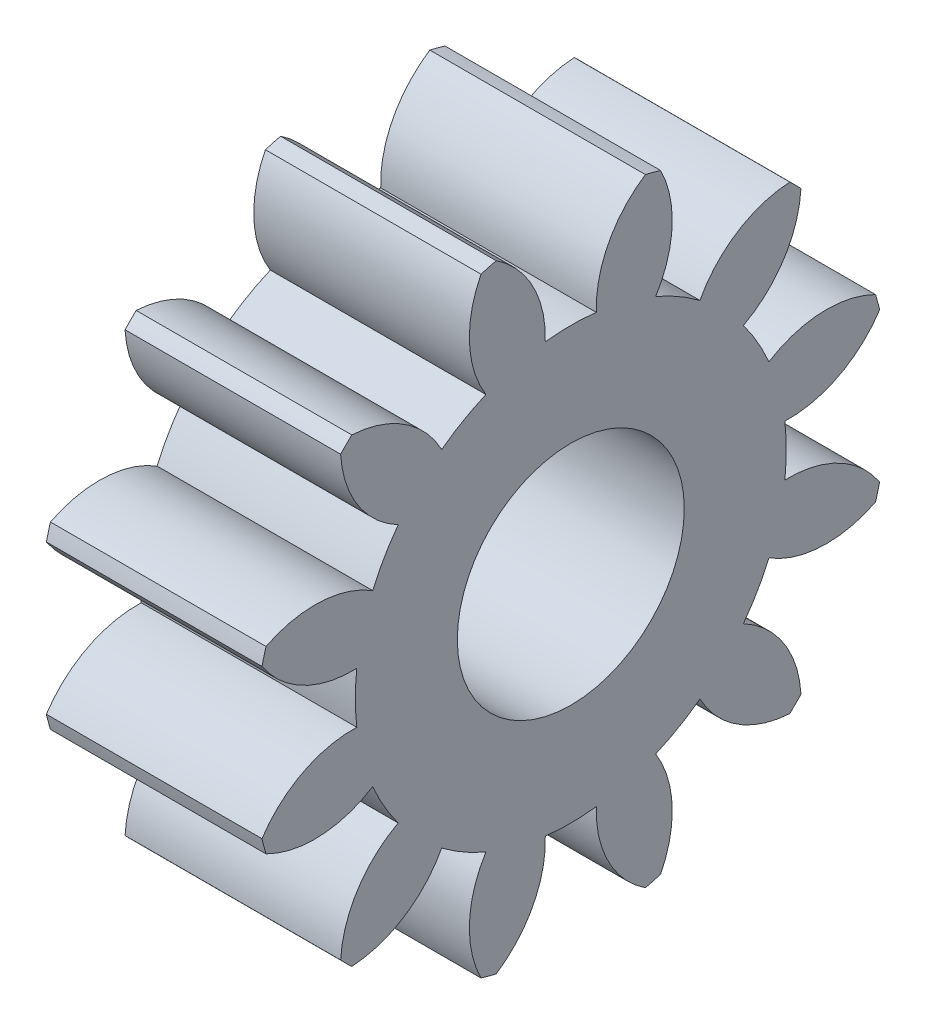
SolidWorks part; units mm, degrees
ref_plane "Plane1" through (0, 0, 0) normal (0, 0, 1) x (1, 0, 0)
ref_plane "Plane2" through (0, 0, 0) normal (0, 1, 0) x (1, 0, 0)
ref_plane "Plane3" through (0, 0, 0) normal (1, 0, 0) x (0, 0, -1)
sketch "HoldingSke" plane through (0, 0, 0) normal (0, 1, 0) x (1, 0, 0)
  line L0 (0, 0) -> (0.9781, -0.2079)
  line L1 (-15, 0) -> (100, 0) construction
  line L2 (0, 0) -> (-2.1039, 2.3779)
  line L3 (0, 0) -> (-11.863, 4.5341)
  line L4 (0, 0) -> (8.4473, 1.7955)
  line L5 (0, 0) -> (-46.8476, -17.4728)
  line L6 (0, 0) -> (-4.1448, -2.7965)
  line L7 (-2.1039, 2.3779) -> (8.6586, 51.2059)
  line L8 (-76.2, 54.61) -> (-75.3, 54.61)
  line L9 (-71.009, 38.7566) -> (-53.1078, 45.2721)
  line L10 (-76.2, 71.12) -> (104.1128, 71.12)
  line L11 (0, 0) -> (-5, 0)
  line L12 (-76.2, 101.6) -> (-76.162, 101.6)
  line L13 (24.9733, 27.94) -> (52.9518, 28.4284)
  line L14 (24.9733, 27.94) -> (24.9743, 27.94)
  line L15 (24.9733, 27.94) -> (100.4006, 29.5858)
  line L16 (-63.627, -1) -> (-12.827, -1)
  circle A0 centre (0, 0) radius 2.5
  circle A1 centre (0, 0) radius 4.749
  circle A2 centre (0, 0) radius 37.5
  circle A3 centre (0, 0) radius 2.5
  dimension "MHD" = 9.498
  dimension "Hub_dia" = 75
  dimension "Bore" = 5
  dimension "MBD" = 5
  dimension "Num_teeth" = 12
  dimension "Pitch" = 1
  dimension "Overall_len" = 50
  dimension "Show_teeth" = 12
  dimension "Thickness" = 5
  dimension "OAL" = 50.0001
  dimension "T_dim" = 0.9
  dimension "Ap" = 20
  dimension "H" = 19.05
  dimension "Pitch_radius" = 180.3128
  dimension "Width" = 5
  dimension "Backlash" = 0.038
  dimension "Addendum_fac" = 1
  dimension "Dedendum_fac" = 1.25
  dimension "Clearance_fac" = 0.25
  dimension "Dedendum_add" = 0.001
  dimension "Module" = 1
sketch "BasProSke" plane through (0, 0, 0) normal (0, 1, 0) x (1, 0, 0)
  line L0 (-10, 0) -> (60, 0) construction
  line L1 (0, 0) -> (0, 7)
  line L2 (0, 0) -> (5, 0)
  line L3 (5, 0) -> (5, 7)
  line L4 (5, 7) -> (0, 7)
  dimension "Thickness" = 5
  dimension "Diameter" = 14
revolve "Base-Revolve" add sketch "BasProSke" angle 360 about L0
sketch "TooCutSke" plane through (0, 0, 0) normal (1, 0, 0) x (0, 0, -1)
  line L1 (0, 0) -> (0, 107) construction
  line L2 (0, 0) -> (-0.8496, 5.9395) construction
  line L3 (0, 0) -> (-3.0836, 11.5081) construction
  line L4 (-0.8496, 5.9395) -> (-1.5418, 5.7541) construction
  arc A0 (0.5622, 4.7156) -> (-0.5622, 4.7156) centre (0, 0) ccw
  arc A1 (1.6729, 6.8233) -> (-1.6729, 6.8233) centre (0, 0) ccw
  circle A2 centre (0, 0) radius 6 construction
  circle A3 centre (0, 0) radius 5.6382 construction
  arc A4 (-0.5622, 4.7156) -> (-1.6729, 6.8233) centre (-2.9608, 4.7982) ccw
  arc A5 (1.6729, 6.8233) -> (0.5622, 4.7156) centre (2.9608, 4.7982) ccw
  dimension "Root_dia" = 9.498
  dimension "Overcut_dia" = 14.0508
  dimension "Pitch_dia" = 12
  dimension "Base_dia" = 11.2763
  dimension "Flank_rad" = 2.4
  dimension "Half_ang" = 15
  dimension "Half_CT" = 0.7167
extrude "ToothCut" cut sketch "TooCutSke" along normal through all
fillet "Breaks" [suppressed] radius 0.02
fillet "RootFillets" [suppressed] radius 0.251
pattern_circular "TeethCuts" count 12 every 30 about axis through (-10, 0, 0) along (1, 0, 0) of "ToothCut", "RootFillets", "Breaks"
sketch "HubNeaOneSke" plane through (0, 0, 0) normal (-1, 0, 0) x (0, 0, 1)
  circle A0 centre (0, 0) radius 4.749
  dimension "Diameter" = 9.498
extrude "HubNearOne" [suppressed] add sketch "HubNeaOneSke" along normal blind 45.0001
sketch "HubNeaBotSke" plane through (0, 0, 0) normal (-1, 0, 0) x (0, 0, 1)
  circle A0 centre (0, 0) radius 4.749
  dimension "Diameter" = 9.498
extrude "HubNearBoth" [suppressed] add sketch "HubNeaBotSke" along normal blind 22.5
ref_plane "FarPln" through (5, 0, 0) normal (1, 0, 0) x (0, 0, -1)
sketch "HubFarSke" plane through (5, 0, 0) normal (1, 0, 0) x (0, 0, -1)
  circle A0 centre (0, 0) radius 4.749
  dimension "Diameter" = 9.498
extrude "HubFar" [suppressed] add sketch "HubFarSke" along normal blind 22.5
sketch "BorSke" plane through (0, 0, 0) normal (1, 0, 0) x (0, 0, -1)
  circle A0 centre (0, 0) radius 2.5
  dimension "Diameter" = 5
extrude "Bore" cut sketch "BorSke" along normal mid plane 100.0001
sketch "KeySke" plane through (0, 0, 0) normal (1, 0, 0) x (0, 0, -1)
  line L0 (-1, 0) -> (-1, 3.4)
  line L1 (-1, 3.4) -> (1, 3.4)
  line L2 (1, 3.4) -> (1, 0)
  line L3 (0, 0) -> (0, 34) construction
  line L4 (-1, 0) -> (1, 0)
  dimension "Offset" = 3.4
  dimension "Width" = 2
extrude "Keyway" [suppressed] cut sketch "KeySke" along normal mid plane 100.0001
pattern_circular "Keyway2" [suppressed] count 2 every 90 about axis through (-10, 0, 0) along (1, 0, 0)
sketch "Sketch1" plane through (5, 0, 0) normal (1, 0, 0) x (0, 0, -1)
  line L1 (-7.544, 8.2817) -> (12.5457, 8.2817)
  line L2 (-7.544, 8.2817) -> (-7.544, -9.0559)
  line L3 (-7.544, -9.0559) -> (12.5457, -9.0559)
  line L4 (12.5457, 8.2817) -> (12.5457, -9.0559)
extrude "Cut-Extrude3" cut sketch "Sketch1" against normal blind 0.25
equation "' \"Module@HoldingSke\" = 6.35"
equation "' \"Num_teeth@HoldingSke\" = 12"
equation "' \"Ap@HoldingSke\" =  20"
equation "' \"Ap@HoldingSke\" = 20"
equation "' \"Width@HoldingSke\" = 0.5 * 25.4"
equation "' \"Hub_dia@HoldingSke\"= 1 * 25.4"
equation "' \"Hub_dia@HoldingSke\" = 1 * 25.4"
equation "' \"Overall_len@HoldingSke\" = 1.0 * 25.4"
equation "' \"Bore@HoldingSke\" = 0.75 * 25.4"
equation "' \"T_dim@HoldingSke\" = 0.1 * 25.4"
equation "' \"Width@KeySke\" = 0.25 * 25.4"
equation "' \"Show_teeth@HoldingSke\" = 13"
equation "' \"Backlash@HoldingSke\" = 0.009 * 25.4"
equation "' \"Addendum_fac@HoldingSke\" = 1.0"
equation "' \"Dedendum_fac@HoldingSke\" = 1.25"
equation "' \"Dedendum_add@HoldingSke\" = 0.00005 * 25.4"
equation "' \"Clearance_fac@HoldingSke\" = 0.25"
equation "\"Pitch@HoldingSke\" = 1 / \"Module@HoldingSke\""
equation "\"Overcut_dia@TooCutSke\" = (\"Num_teeth@HoldingSke\" + 2 * \"Addendum_fac@HoldingSke\") / \"Pitch@HoldingSke\" + 0.002 * 25.4"
equation "\"Pitch_dia@TooCutSke\" = \"Num_teeth@HoldingSke\" / \"Pitch@HoldingSke\""
equation "\"Base_dia@TooCutSke\" = \"Num_teeth@HoldingSke\" / \"Pitch@HoldingSke\" * cos((\"Ap@HoldingSke\"  * 3.14159265 / 180))"
equation "\"Root_dia@TooCutSke\" = (\"Num_teeth@HoldingSke\" + 2) / \"Pitch@HoldingSke\" - 2 * (\"Addendum_fac@HoldingSke\" + \"Dedendum_fac@HoldingSke\") / \"Pitch@HoldingSke\" - \"Dedendum_add@HoldingSke\" * 2"
equation "\"Half_ang@TooCutSke\" = 180 / \"Num_teeth@HoldingSke\""
equation "\"Half_CT@TooCutSke\" = \"Num_teeth@HoldingSke\" / \"Pitch@HoldingSke\" * sin((3.14159265 / 2 / \"Num_teeth@HoldingSke\")) / 2 - 7 * \"Backlash@HoldingSke\" / 4"
equation "\"Flank_rad@TooCutSke\" = \"Num_teeth@HoldingSke\" / \"Pitch@HoldingSke\" / 5"
equation "\"Radius@RootFillets\" = \"Clearance_fac@HoldingSke\" / \"Pitch@HoldingSke\" + \"Dedendum_add@HoldingSke\""
equation "\"Break_rad@Breaks\" = 0.02 / \"Pitch@HoldingSke\""
equation "\"Thickness@HoldingSke\" = \"Width@HoldingSke\""
equation "\"OAL@HoldingSke\" = \"Thickness@HoldingSke\""
equation "\"MHD@HoldingSke\" = (\"Num_teeth@HoldingSke\" + 2) / \"Pitch@HoldingSke\" - 2 * (\"Addendum_fac@HoldingSke\" + \"Dedendum_fac@HoldingSke\")  / \"Pitch@HoldingSke\" - \"Dedendum_add@HoldingSke\" * 2"
equation "\"MBD@HoldingSke\" = (\"Num_teeth@HoldingSke\" + 2) / \"Pitch@HoldingSke\" - 2 * (\"Addendum_fac@HoldingSke\" + \"Dedendum_fac@HoldingSke\")  / \"Pitch@HoldingSke\" - \"Dedendum_add@HoldingSke\" * 2 - 0.002 * 25.4"
equation "\"MHD@HoldingSke\" = ((sgn( \"MHD@HoldingSke\" - \"Hub_dia@HoldingSke\" )-1)*( \"MHD@HoldingSke\" - \"Hub_dia@HoldingSke\" ))/-2+ \"Hub_dia@HoldingSke\""
equation "\"MBD@HoldingSke\" = ((sgn( \"MBD@HoldingSke\" - \"Bore@HoldingSke\" )-1)*( \"MBD@HoldingSke\" - \"Bore@HoldingSke\" ))/-2+ \"Bore@HoldingSke\""
equation "\"OAL@HoldingSke\" = ((sgn( \"OAL@HoldingSke\" - \"Overall_len@HoldingSke\" )+1)*( \"OAL@HoldingSke\" - \"Overall_len@HoldingSke\" ))/2 + \"Overall_len@HoldingSke\" + 0.000002 * 25.4"
equation "\"Num_teeth@TeethCuts\" = int( \"Show_teeth@HoldingSke\" ) + 1"
equation "\"Num_teeth@TeethCuts\" = ((sgn( \"Num_teeth@TeethCuts\" - \"Num_teeth@HoldingSke\" )-1)*( \"Num_teeth@TeethCuts\" - \"Num_teeth@HoldingSke\" ))/-2+ \"Num_teeth@HoldingSke\""
equation "\"Num_teeth@TeethCuts\" = ((sgn( \"Num_teeth@TeethCuts\" - 2.0)+1)*( \"Num_teeth@TeethCuts\" - 2.0))/2 +2.0"
equation "\"Angle@TeethCuts\" = 360.0 / \"Num_teeth@HoldingSke\""
equation "\"Diameter@BasProSke\" = (\"Num_teeth@HoldingSke\" + 2 * \"Addendum_fac@HoldingSke\") / \"Pitch@HoldingSke\""
equation "\"Thickness@BasProSke\"  = \"Thickness@HoldingSke\""
equation "' \"Fillet_rad@BasProSke\" =  \"Thickness@HoldingSke\" * 0.05"
equation "' \"Fillet_rad@BasProSke\" = \"Thickness@HoldingSke\" * 0.05"
equation "\"MHD@HoldingSke\" = ((sgn( \"MHD@HoldingSke\" - \"Root_dia@TooCutSke\" )-1)*( \"MHD@HoldingSke\" - \"Root_dia@TooCutSke\" ))/-2+ \"Root_dia@TooCutSke\""
equation "\"Diameter@HubNeaOneSke\" = \"MHD@HoldingSke\""
equation "\"Length@HubNearOne\" = \"OAL@HoldingSke\" - \"Thickness@BasProSke\""
equation "\"Diameter@HubNeaBotSke\" = \"MHD@HoldingSke\""
equation "\"Length@HubNearBoth\" = ( \"OAL@HoldingSke\" - \"Thickness@BasProSke\" ) / 2.0"
equation "\"Thickness@FarPln\" = \"Thickness@BasProSke\""
equation "\"Diameter@HubFarSke\" = \"MHD@HoldingSke\""
equation "\"Length@HubFar\" = ( \"OAL@HoldingSke\" - \"Thickness@BasProSke\" ) / 2.0"
equation "\"Diameter@BorSke\" = \"MBD@HoldingSke\""
equation "\"D1@Bore\" = \"OAL@HoldingSke\" * 2.0"
equation "\"D1@Keyway\" = \"OAL@HoldingSke\" * 2.0"
equation "\"Offset@KeySke\" = \"T_dim@HoldingSke\" + \"MBD@HoldingSke\" / 2.0"
